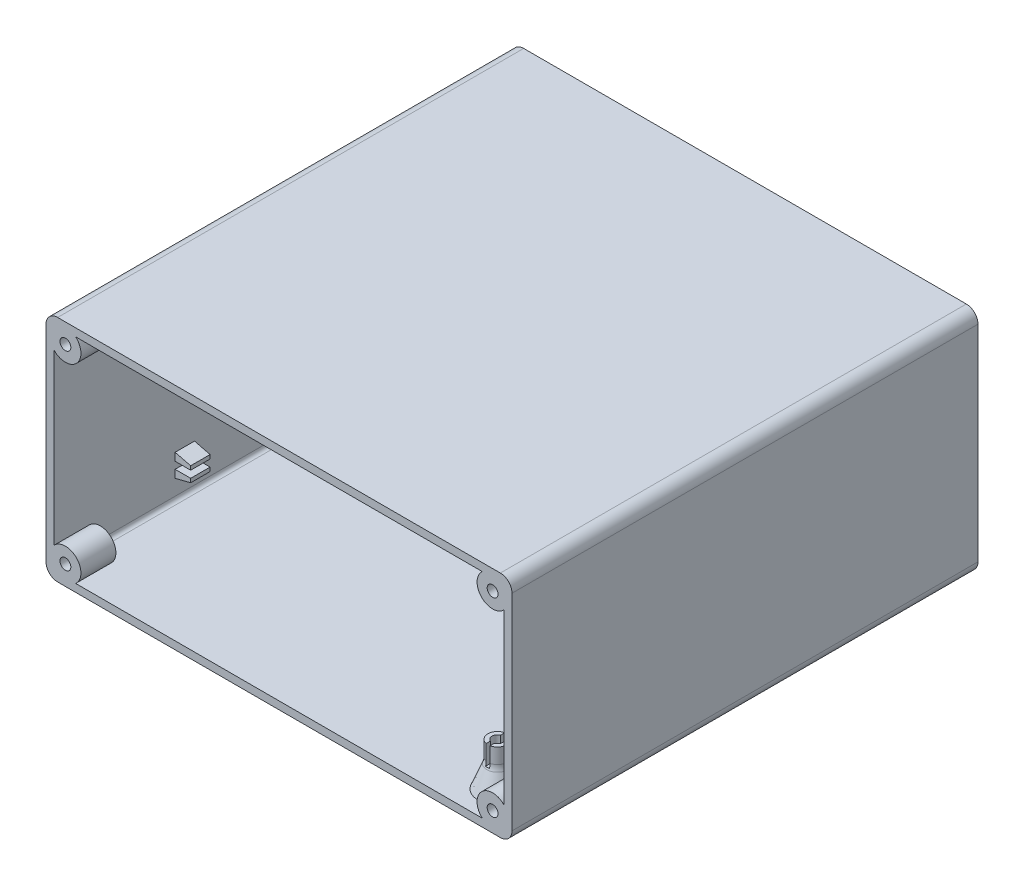
SolidWorks part; units mm, degrees
ref_plane "前视基准面" through (0, 0, 0) normal (0, 0, 1) x (1, 0, 0)
ref_plane "上视基准面" through (0, 0, 0) normal (0, 1, 0) x (1, 0, 0)
ref_plane "右视基准面" through (0, 0, 0) normal (1, 0, 0) x (0, 0, -1)
sketch "草图1" plane through (0, 0, 0) normal (0, 0, 1) x (1, 0, 0)
  line L8 (-919.2874, -10.5411) -> (-919.2874, 18.4589) construction
  line L9 (-976.2874, 27.0589) -> (-862.2874, 27.0589)
  line L10 (-979.2874, 24.0589) -> (-979.2874, -28.9411)
  line L11 (-976.2874, -31.9411) -> (-862.2874, -31.9411)
  line L12 (-859.2874, 24.0589) -> (-859.2874, -28.9411)
  line L13 (-979.2874, 27.0589) -> (-859.2874, -31.9411) construction
  line L14 (-979.2874, -31.9411) -> (-859.2874, 27.0589) construction
  line L16 (-976.2874, 25.0589) -> (-862.2874, 25.0589)
  line L17 (-977.2874, 24.0589) -> (-977.2874, -28.9411)
  line L18 (-976.2874, -29.9411) -> (-862.2874, -29.9411)
  line L19 (-861.2874, 24.0589) -> (-861.2874, -28.9411)
  line L20 (-977.2874, 25.0589) -> (-861.2874, -29.9411) construction
  line L21 (-977.2874, -29.9411) -> (-861.2874, 25.0589) construction
  arc A0 (-979.2874, -28.9411) -> (-976.2874, -31.9411) centre (-976.2874, -28.9411) ccw
  arc A1 (-862.2874, -31.9411) -> (-859.2874, -28.9411) centre (-862.2874, -28.9411) ccw
  arc A2 (-862.2874, 27.0589) -> (-859.2874, 24.0589) centre (-862.2874, 24.0589) cw
  arc A3 (-976.2874, 27.0589) -> (-979.2874, 24.0589) centre (-976.2874, 24.0589) ccw
  arc A4 (-977.2874, -28.9411) -> (-976.2874, -29.9411) centre (-976.2874, -28.9411) ccw
  arc A5 (-862.2874, -29.9411) -> (-861.2874, -28.9411) centre (-862.2874, -28.9411) ccw
  arc A6 (-862.2874, 25.0589) -> (-861.2874, 24.0589) centre (-862.2874, 24.0589) cw
  arc A7 (-976.2874, 25.0589) -> (-977.2874, 24.0589) centre (-976.2874, 24.0589) ccw
  point P0 (-919.2874, -2.4411)
  point P19 (-919.2874, -2.4411)
  dimension "D3" = 3
  dimension "D6" = 1
  dimension "D1" = 120
  dimension "D2" = 59
  dimension "D4" = 55
  dimension "D5" = 116
extrude "凸台-拉伸1" add sketch "草图1" along normal blind 120
sketch "草图5" plane through (0, 0, 120) normal (0, 0, 1) x (1, 0, 0)
  line L0 (-919.2874, 36.0204) -> (-919.2874, -6.0143) construction
  line L1 (-985.9227, -2.4411) -> (-883.0425, -2.4411) construction
  circle A0 centre (-974.2916, 22.0537) radius 1.75 construction
  circle A1 centre (-974.2916, 22.0537) radius 1.4
  circle A2 centre (-974.2916, 22.0537) radius 4
  circle A3 centre (-864.2832, 22.0537) radius 1.75 construction
  circle A4 centre (-864.2832, 22.0537) radius 4
  circle A5 centre (-864.2832, 22.0537) radius 1.4
  circle A6 centre (-864.2832, -26.936) radius 1.75 construction
  circle A7 centre (-864.2832, -26.936) radius 1.4
  circle A8 centre (-864.2832, -26.936) radius 4
  circle A9 centre (-974.2916, -26.936) radius 1.75 construction
  circle A10 centre (-974.2916, -26.936) radius 4
  circle A11 centre (-974.2916, -26.936) radius 1.4
  dimension "D1" = 3.5
  dimension "D2" = 2.8
extrude "凸台-拉伸3" add sketch "草图5" against normal blind 9
sketch "草图6" plane through (0, 0, 0) normal (0, 0, -1) x (-1, 0, 0)
  line L0 (919.2874, 33.9453) -> (919.2874, -6.0143) construction
  line L1 (854.7114, -2.4411) -> (971.8155, -2.4411) construction
  line L4 (979.2874, -28.9411) -> (979.2874, 24.0589)
  line L5 (976.2874, 27.0589) -> (862.2874, 27.0589)
  line L6 (859.2874, 24.0589) -> (859.2874, -28.9411)
  line L7 (862.2874, -31.9411) -> (976.2874, -31.9411)
  line L8 (979.2874, -28.9411) -> (979.2874, 24.0589)
  line L9 (976.2874, 27.0589) -> (862.2874, 27.0589)
  line L10 (859.2874, 24.0589) -> (859.2874, -28.9411)
  line L11 (862.2874, -31.9411) -> (976.2874, -31.9411)
  circle A0 centre (864.2832, 22.0537) radius 1.4 construction
  circle A1 centre (864.2832, 22.0537) radius 1.4
  circle A2 centre (864.2832, 22.0537) radius 1.4
  circle A3 centre (864.2832, 22.0537) radius 4
  arc A4 (976.2874, -31.9411) -> (979.2874, -28.9411) centre (976.2874, -28.9411) ccw
  arc A5 (979.2874, 24.0589) -> (976.2874, 27.0589) centre (976.2874, 24.0589) ccw
  arc A6 (862.2874, 27.0589) -> (859.2874, 24.0589) centre (862.2874, 24.0589) ccw
  arc A7 (859.2874, -28.9411) -> (862.2874, -31.9411) centre (862.2874, -28.9411) ccw
  arc A8 (976.2874, -31.9411) -> (979.2874, -28.9411) centre (976.2874, -28.9411) ccw
  arc A9 (979.2874, 24.0589) -> (976.2874, 27.0589) centre (976.2874, 24.0589) ccw
  arc A10 (862.2874, 27.0589) -> (859.2874, 24.0589) centre (862.2874, 24.0589) ccw
  arc A11 (859.2874, -28.9411) -> (862.2874, -31.9411) centre (862.2874, -28.9411) ccw
  circle A12 centre (974.2916, 22.0537) radius 1.4
  circle A13 centre (974.2916, 22.0537) radius 4
  circle A14 centre (974.2916, -26.936) radius 4
  circle A15 centre (974.2916, -26.936) radius 1.4
  circle A16 centre (864.2832, -26.936) radius 1.4
  circle A17 centre (864.2832, -26.936) radius 4
  dimension "D1" = 0
extrude "凸台-拉伸4" add sketch "草图6" against normal blind 9 contours A17 | A13 | A14 | A3 | A1 | A16 | A15 | A12
ref_plane "基准面2" through (0, 0, 60) normal (0, 0, 1) x (1, 0, 0)
sketch "草图7" plane through (0, 0, 60) normal (0, 0, 1) x (1, 0, 0)
  line L0 (-919.2874, 32.3284) -> (-919.2874, -22.6809) construction
  line L1 (-972.7039, 19.3037) -> (-971.1161, 22.0537)
  line L2 (-971.1161, 22.0537) -> (-972.7039, 24.8037)
  line L3 (-972.7039, 24.8037) -> (-975.8793, 24.8037)
  line L4 (-975.8793, 24.8037) -> (-977.467, 22.0537)
  line L5 (-977.467, 22.0537) -> (-975.8793, 19.3037)
  line L6 (-975.8793, 19.3037) -> (-972.7039, 19.3037)
  line L7 (-984.1673, -2.4411) -> (-882.0214, -2.4411) construction
  line L8 (-862.6955, 19.3037) -> (-865.8709, 19.3037)
  line L9 (-861.1078, 22.0537) -> (-862.6955, 19.3037)
  line L10 (-862.6955, 24.8037) -> (-861.1078, 22.0537)
  line L11 (-865.8709, 24.8037) -> (-862.6955, 24.8037)
  line L12 (-867.4586, 22.0537) -> (-865.8709, 24.8037)
  line L13 (-865.8709, 19.3037) -> (-867.4586, 22.0537)
  line L14 (-865.8709, -24.186) -> (-867.4586, -26.936)
  line L15 (-867.4586, -26.936) -> (-865.8709, -29.686)
  line L16 (-865.8709, -29.686) -> (-862.6955, -29.686)
  line L17 (-862.6955, -29.686) -> (-861.1078, -26.936)
  line L18 (-861.1078, -26.936) -> (-862.6955, -24.186)
  line L19 (-862.6955, -24.186) -> (-865.8709, -24.186)
  line L20 (-975.8793, -24.186) -> (-972.7039, -24.186)
  line L21 (-977.467, -26.936) -> (-975.8793, -24.186)
  line L22 (-975.8793, -29.686) -> (-977.467, -26.936)
  line L23 (-972.7039, -29.686) -> (-975.8793, -29.686)
  line L24 (-971.1161, -26.936) -> (-972.7039, -29.686)
  line L25 (-972.7039, -24.186) -> (-971.1161, -26.936)
  circle A0 centre (-974.2916, 22.0537) radius 1.4 construction
  circle A1 centre (-974.2916, 22.0537) radius 1.4 construction
  circle A2 centre (-974.2916, 22.0537) radius 2.75 construction
  circle A3 centre (-864.2832, 22.0537) radius 2.75 construction
  circle A4 centre (-864.2832, 22.0537) radius 1.4 construction
  circle A5 centre (-864.2832, -26.936) radius 1.4 construction
  circle A6 centre (-864.2832, -26.936) radius 2.75 construction
  circle A7 centre (-974.2916, -26.936) radius 2.75 construction
  circle A8 centre (-974.2916, -26.936) radius 1.4 construction
  dimension "D1" = 5.5
extrude "切除-拉伸1" cut sketch "草图7" against normal mid plane 108
sketch "草图8" plane through (0, 0, 60) normal (0, 0, 1) x (1, 0, 0)
  line L0 (-977.2874, 21.7426) -> (-977.2874, 22.3648)
  line L4 (-977.2874, 22.3648) -> (-977.467, 22.0537)
  line L5 (-977.467, 22.0537) -> (-977.2874, 21.7426)
  line L7 (-919.2874, 27.0589) -> (-919.2874, -17.0585) construction
  line L8 (-971.91, 23.4287) -> (-972.7039, 24.8037) [skipped]
  line L9 (-974.2916, 24.8037) -> (-975.8793, 24.8037) [skipped]
  line L10 (-972.7039, 19.3037) -> (-971.91, 20.6787) [skipped]
  line L11 (-974.2916, 19.3037) -> (-972.7039, 19.3037) [skipped]
  line L12 (-862.2874, 27.0589) -> (-976.2874, 27.0589) construction
  line L13 (-979.2874, -2.4411) -> (-889.6622, -2.4411) construction
  line L14 (-979.2874, 24.0589) -> (-979.2874, -28.9411) construction
  line L15 (-861.1078, 22.0537) -> (-861.2874, 21.7426)
  line L16 (-861.2874, 22.3648) -> (-861.1078, 22.0537)
  line L17 (-861.2874, 21.7426) -> (-861.2874, 22.3648)
  line L18 (-861.2874, -26.6249) -> (-861.2874, -27.2471)
  line L19 (-861.2874, -27.2471) -> (-861.1078, -26.936)
  line L20 (-861.1078, -26.936) -> (-861.2874, -26.6249)
  line L21 (-977.467, -26.936) -> (-977.2874, -26.6249)
  line L22 (-977.2874, -27.2471) -> (-977.467, -26.936)
  line L23 (-977.2874, -26.6249) -> (-977.2874, -27.2471)
  circle A0 centre (-974.2916, 22.0537) radius 1.4 construction
  circle A1 centre (-974.2916, 22.0537) radius 1.4 construction
  dimension "D1" = 1.8204
extrude "凸台-拉伸5" add sketch "草图8" along normal mid plane 96
ref_plane "基准面3" through (-871.5374, 0, 0) normal (-1, 0, 0) x (0, 0, 1)
sketch "草图9" plane through (-871.5374, 0, 0) normal (-1, 0, 0) x (0, 0, 1)
  line L0 (61, -29.9411) -> (61, -18.8838)
  line L1 (111, -29.9411) -> (9, -29.9411) construction
  line L2 (61, -18.8838) -> (58.55, -18.8838)
  line L3 (58.55, -18.8838) -> (58.55, -22.8108)
  line L4 (58.2625, -24.2998) -> (56, -29.9411)
  line L5 (56, -29.9411) -> (61, -29.9411)
  line L6 (86.25, -29.9411) -> (86.25, -9.34) construction
  line L7 (120, -28.9411) -> (120, 24.0589) construction
  arc A0 (58.55, -22.8108) -> (58.2625, -24.2998) centre (54.55, -22.8108) cw
  dimension "D5" = 4
  dimension "D1" = 59
  dimension "D2" = 2.45
  dimension "D3" = 11.0573
  dimension "D4" = 5
  dimension "D6" = 33.75
revolve "旋转1" add sketch "草图9" angle 360 about L0
ref_plane "基准面4" through (0, 0, 86.25) normal (0, 0, 1) x (1, 0, 0)
sketch "草图10" plane through (0, -18.8838, 0) normal (0, 1, 0) x (1, 0, 0)
  line L0 (-872.0374, -62.3077) -> (-872.0374, -64.2169)
  line L1 (-872.0374, -57.7831) -> (-871.0374, -57.7831)
  line L2 (-872.0374, -57.7831) -> (-872.0374, -59.6923)
  line L3 (-872.0374, -64.2169) -> (-871.0374, -64.2169)
  line L4 (-871.0374, -57.7831) -> (-871.0374, -59.6923)
  line L5 (-872.0374, -57.7831) -> (-871.0374, -64.2169) construction
  line L6 (-872.0374, -64.2169) -> (-871.0374, -57.7831) construction
  line L7 (-871.0374, -62.3077) -> (-871.0374, -64.2169)
  arc A0 (-872.0374, -59.6923) -> (-872.0374, -62.3077) centre (-871.5374, -61) ccw
  circle A1 centre (-871.5374, -61) radius 2.45
  circle A2 centre (-871.5374, -61) radius 2.45 construction
  arc A3 (-871.0374, -62.3077) -> (-871.0374, -59.6923) centre (-871.5374, -61) ccw
  dimension "D3" = 2.8
  dimension "D2" = 1
  dimension "D1" = 0
extrude "切除-拉伸2" cut sketch "草图10" against normal blind 5
mirror "镜向3" about plane through (0, 0, 86.25) normal (0, 0, 1) of "切除-拉伸2", "旋转1"
sketch "草图11" plane through (0, 0, 86.25) normal (0, 0, 1) x (1, 0, 0)
  line L0 (-977.2874, 19.4032) -> (-977.2874, -24.2855) construction
  line L1 (-977.2874, -19.136) -> (-973.2874, -20.136)
  line L2 (-977.2874, -19.136) -> (-977.2874, -21.136)
  line L3 (-977.2874, -21.136) -> (-973.2874, -21.136)
  line L4 (-973.2874, -20.136) -> (-973.2874, -21.136)
  line L7 (-977.2874, -22.936) -> (-973.2874, -22.936)
  line L8 (-977.2874, -22.936) -> (-977.2874, -24.936)
  line L9 (-977.2874, -24.936) -> (-973.2874, -23.936)
  line L10 (-973.2874, -22.936) -> (-973.2874, -23.936)
  arc A0 (-971.6517, -29.9411) -> (-977.2874, -24.2855) centre (-974.2916, -26.936) ccw construction
  point P0 (-975.5374, -20.136)
  point P5 (-975.5374, -23.936)
  dimension "D1" = 2
  dimension "D2" = 2
  dimension "D3" = 1
  dimension "D4" = 4
  dimension "D5" = 1.8
  dimension "D6" = 1
  dimension "D7" = 4
extrude "凸台-拉伸6" add sketch "草图11" along normal mid plane 5
sketch "草图12" plane through (0, -31.9411, 0) normal (0, -1, 0) x (1, 0, 0)
  circle A0 centre (-871.5374, 111.5) radius 2.7375 construction
  circle A1 centre (-871.5374, 61) radius 2.7375 construction
  circle A2 centre (-871.5374, 111.5) radius 2.7375 construction
  circle A3 centre (-871.5374, 61) radius 2.7375 construction
  circle A4 centre (-871.5374, 61) radius 1.4
  circle A5 centre (-871.5374, 111.5) radius 1.4
extrude "切除-拉伸3" cut sketch "草图12" against normal blind 10
sketch "草图13" plane through (0, -31.9411, 0) normal (0, -1, 0) x (-1, 0, 0)
  circle A0 centre (871.5374, -61) radius 2.6
  circle A1 centre (871.5374, -111.5) radius 2.6
  circle A3 centre (871.5374, -61) radius 2.7375 construction
  circle A5 centre (871.5374, -111.5) radius 2.7375 construction
  dimension "D1" = 5.2
  dimension "D2" = 5.2
extrude "切除-拉伸4" cut sketch "草图13" against normal blind 2.5
sketch "草图15" plane through (-979.2874, 0, 0) normal (-1, 0, 0) x (0, 0, 1)
  circle A0 centre (38.3543, -2.3305) radius 15 construction
  circle A1 centre (38.3543, -2.3305) radius 1
  circle A2 centre (38.3543, 0.6695) radius 1
  circle A3 centre (38.3543, 3.6695) radius 1
  circle A4 centre (38.3543, 6.6695) radius 1
  circle A5 centre (38.3543, 9.6695) radius 1
  circle A6 centre (38.3543, 12.6695) radius 1
  circle A7 centre (41.6921, 12.2934) radius 1
  circle A8 centre (44.8626, 11.184) radius 1
  circle A9 centre (47.7066, 9.3969) radius 1
  circle A10 centre (50.0818, 7.0218) radius 1
  circle A11 centre (51.8688, 4.1777) radius 1
  circle A12 centre (52.9782, 1.0073) radius 1
  circle A13 centre (53.3543, -2.3305) radius 1
  circle A14 centre (52.9782, -5.6684) radius 1
  circle A15 centre (51.8688, -8.8388) radius 1
  circle A16 centre (50.0818, -11.6829) radius 1
  circle A17 centre (47.7066, -14.058) radius 1
  circle A18 centre (44.8626, -15.8451) radius 1
  circle A19 centre (41.6921, -16.9545) radius 1
  circle A20 centre (38.3543, -17.3305) radius 1
  circle A21 centre (35.0165, -16.9545) radius 1
  circle A22 centre (31.846, -15.8451) radius 1
  circle A23 centre (29.002, -14.058) radius 1
  circle A24 centre (26.6268, -11.6829) radius 1
  circle A25 centre (24.8398, -8.8388) radius 1
  circle A26 centre (23.7304, -5.6684) radius 1
  circle A27 centre (23.3543, -2.3305) radius 1
  circle A28 centre (23.7304, 1.0073) radius 1
  circle A29 centre (24.8398, 4.1777) radius 1
  circle A30 centre (26.6268, 7.0218) radius 1
  circle A31 centre (41.5919, 9.2245) radius 1
  circle A32 centre (44.5893, 7.9225) radius 1
  circle A33 centre (47.1243, 5.8601) radius 1
  circle A34 centre (49.0089, 3.1902) radius 1
  circle A35 centre (50.1033, 0.1109) radius 1
  circle A36 centre (50.3263, -3.1494) radius 1
  circle A37 centre (49.6614, -6.3491) radius 1
  circle A38 centre (48.1579, -9.2507) radius 1
  circle A39 centre (45.9274, -11.6391) radius 1
  circle A40 centre (43.1351, -13.3371) radius 1
  circle A41 centre (39.9883, -14.2188) radius 1
  circle A42 centre (36.7203, -14.2188) radius 1
  circle A43 centre (33.5735, -13.3371) radius 1
  circle A44 centre (30.7812, -11.6391) radius 1
  circle A45 centre (28.5507, -9.2507) radius 1
  circle A46 centre (27.0472, -6.3491) radius 1
  circle A47 centre (26.3823, -3.1494) radius 1
  circle A48 centre (26.6053, 0.1109) radius 1
  circle A49 centre (27.6997, 3.1902) radius 1
  circle A50 centre (41.6055, 6.0617) radius 1
  circle A51 centre (44.4176, 4.3205) radius 1
  circle A52 centre (46.4108, 1.6811) radius 1
  circle A53 centre (47.3159, -1.5001) radius 1
  circle A54 centre (47.0107, -4.7935) radius 1
  circle A55 centre (45.5365, -7.7543) radius 1
  circle A56 centre (43.0922, -9.9825) radius 1
  circle A57 centre (40.008, -11.1773) radius 1
  circle A58 centre (36.7006, -11.1773) radius 1
  circle A59 centre (33.6164, -9.9825) radius 1
  circle A60 centre (31.1721, -7.7543) radius 1
  circle A61 centre (29.6979, -4.7935) radius 1
  circle A62 centre (29.3927, -1.5001) radius 1
  circle A63 centre (30.2978, 1.6811) radius 1
  circle A64 centre (41.3543, 2.8656) radius 1
  circle A65 centre (43.5504, 0.6695) radius 1
  circle A66 centre (44.3543, -2.3305) radius 1
  circle A67 centre (43.5504, -5.3305) radius 1
  circle A68 centre (41.3543, -7.5267) radius 1
  circle A69 centre (38.3543, -8.3305) radius 1
  circle A70 centre (35.3543, -7.5267) radius 1
  circle A71 centre (33.1581, -5.3305) radius 1
  circle A72 centre (32.3543, -2.3305) radius 1
  circle A73 centre (33.1581, 0.6695) radius 1
  circle A74 centre (35.3543, 2.8656) radius 1
  circle A75 centre (41.2075, -1.4035) radius 1
  circle A76 centre (40.1177, -4.7576) radius 1
  circle A77 centre (36.5909, -4.7576) radius 1
  circle A78 centre (35.5011, -1.4035) radius 1
  circle A79 centre (29.002, 9.3969) radius 1
  circle A80 centre (31.846, 11.184) radius 1
  circle A81 centre (35.0165, 12.2934) radius 1
  circle A82 centre (29.5843, 5.8601) radius 1
  circle A83 centre (32.1193, 7.9225) radius 1
  circle A84 centre (35.1167, 9.2245) radius 1
  circle A85 centre (32.291, 4.3205) radius 1
  circle A86 centre (35.1031, 6.0617) radius 1
  dimension "D1" = 30
  dimension "D2" = 6
  dimension "D3" = 28
  dimension "D4" = 23
  dimension "D5" = 17
  dimension "D6" = 12
  dimension "D7" = 5
extrude "切除-拉伸5" cut sketch "草图15" against normal blind 3
